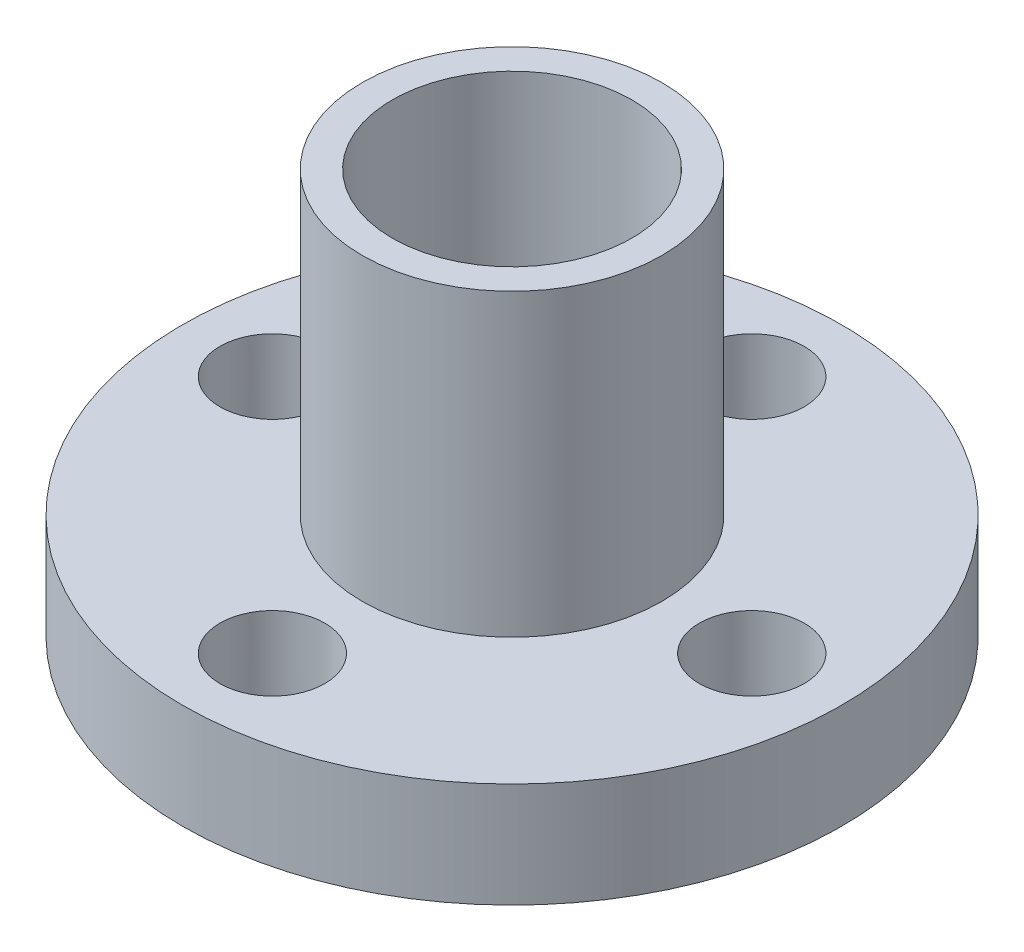
SolidWorks part; units mm, degrees
ref_plane "前视基准面" through (0, 0, 0) normal (0, 0, 1) x (1, 0, 0)
ref_plane "上视基准面" through (0, 0, 0) normal (0, 1, 0) x (1, 0, 0)
ref_plane "右视基准面" through (0, 0, 0) normal (1, 0, 0) x (0, 0, -1)
sketch "草图1" plane through (0, 0, 0) normal (0, 1, 0) x (1, 0, 0)
  circle A0 centre (0, 0) radius 5
  dimension "D1" = 10
extrude "凸台-拉伸1" add sketch "草图1" along normal blind 1.5
sketch "草图2" plane through (0, 1.5, 0) normal (0, 1, 0) x (1, 0, 0)
  circle A0 centre (0, 0) radius 11
  dimension "D1" = 22
extrude "凸台-拉伸2" add sketch "草图2" along normal blind 3.5
sketch "草图3" plane through (0, 5, 0) normal (0, 1, 0) x (1, 0, 0)
  circle A0 centre (0, 0) radius 5
  dimension "D1" = 10
extrude "凸台-拉伸3" add sketch "草图3" along normal blind 10
sketch "草图4" plane through (0, 0, 0) normal (0, -1, 0) x (1, 0, 0)
  circle A0 centre (0, 0) radius 4
extrude "切除-拉伸1" cut sketch "草图4" against normal blind 16
sketch "草图5" plane through (0, 1.5, 0) normal (0, -1, 0) x (1, 0, 0)
  circle A1 centre (8, 0) radius 1.75
  circle A2 centre (0, -8) radius 1.75
  circle A3 centre (-8, 0) radius 1.75
  circle A4 centre (0, 8) radius 1.75
  dimension "D1" = 3.5
  dimension "D2" = 3.5
  dimension "D3" = 3.5
  dimension "D4" = 3.5
extrude "切除-拉伸2" cut sketch "草图5" against normal blind 16
